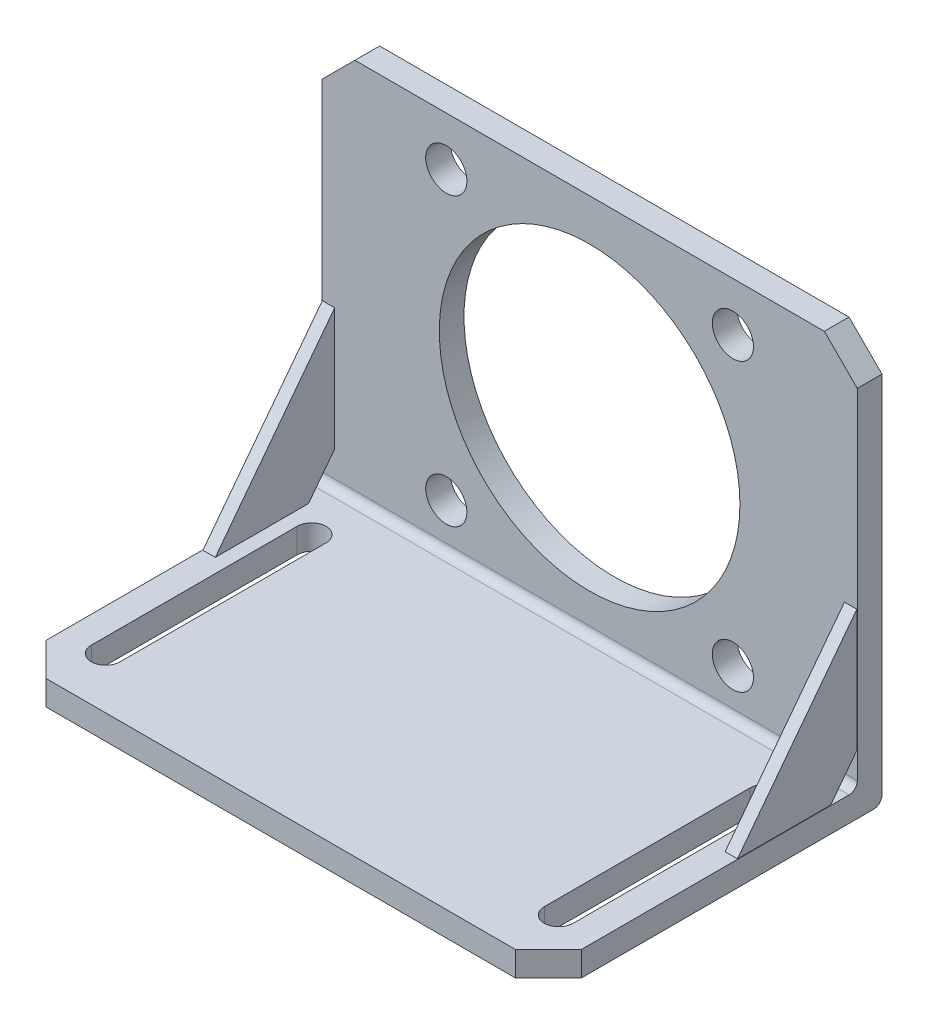
SolidWorks part; units mm, degrees
ref_plane "Front Plane" through (0, 0, 0) normal (0, 0, 1) x (1, 0, 0)
ref_plane "Top Plane" through (0, 0, 0) normal (0, 1, 0) x (1, 0, 0)
ref_plane "Right Plane" through (0, 0, 0) normal (1, 0, 0) x (0, 0, -1)
sketch "Sketch1" plane through (0, 0, 0) normal (0, 0, 1) x (1, 0, 0)
  line L1 (-65.4, -6.042) -> (64.6, -6.042)
  line L2 (-65.4, -6.042) -> (-65.4, 92.458)
  line L3 (-65.4, 92.458) -> (64.6, 92.458)
  line L4 (64.6, -6.042) -> (64.6, 92.458)
  line L6 (-0.4, 91.658) -> (-0.4, -0.042) construction
  line L8 (-35.2, 80.608) -> (34.4, 80.608) construction
  line L9 (-35.2, 80.608) -> (-35.2, 11.008) construction
  line L10 (-35.2, 11.008) -> (34.4, 11.008) construction
  line L11 (34.4, 80.608) -> (34.4, 11.008) construction
  line L12 (-35.2, 80.608) -> (34.4, 11.008) construction
  line L13 (-35.2, 11.008) -> (34.4, 80.608) construction
  circle A0 centre (-0.4, 45.808) radius 36.5
  circle A1 centre (-35.2, 80.608) radius 5
  circle A2 centre (34.4, 80.608) radius 5
  circle A3 centre (34.4, 11.008) radius 5
  circle A4 centre (-35.2, 11.008) radius 5
  arc A5 (34.4, 83.908) -> (34.4, 77.308) centre (34.4, 80.608) ccw construction
  arc A8 (34.4, 14.308) -> (34.4, 7.708) centre (34.4, 11.008) ccw construction
  arc A9 (-35.2, 83.908) -> (-35.2, 77.308) centre (-35.2, 80.608) ccw construction
  arc A10 (34.4, 8.208) -> (34.4, 13.808) centre (34.4, 11.008) ccw construction
  arc A11 (-35.2, 14.308) -> (-35.2, 7.708) centre (-35.2, 11.008) ccw construction
  point P4 (-0.4, -6.042)
  point P5 (0, 0)
  point P6 (0, 0)
  point P19 (0, 0)
  point P20 (0, 0)
  point P27 (0, 49.25)
  point P28 (-0.6, 45.808)
  dimension "D4" = 73
  dimension "D5" = 10
  dimension "D1" = 130
extrude "Boss-Extrude1" add sketch "Sketch1" along normal blind 6
sketch "Sketch2" plane through (0, 0, 6) normal (0, 0, 1) x (1, 0, 0)
  line L0 (64.6, -6.042) -> (64.6, 92.458) construction
  line L1 (-65.4, -6.042) -> (64.6, -6.042)
  line L2 (-65.4, -6.042) -> (-65.4, -0.042)
  line L3 (-65.4, -0.042) -> (64.6, -0.042)
  line L4 (64.6, -6.042) -> (64.6, -0.042)
  dimension "D1" = 6
extrude "Boss-Extrude2" add sketch "Sketch2" along normal blind 75
chamfer "Chamfer1" distance 8 angle 45 4 edges at (64.6, -3.042, 81) (-65.4, -3.042, 81) (64.6, 92.458, 3) (-65.4, 92.458, 3)
sketch "Sketch3" plane through (0, -0.042, 0) normal (0, 1, 0) x (1, 0, 0)
  line L0 (-55.4, -6) -> (-55.4, -81) construction
  line L1 (64.6, -6) -> (-65.4, -6) construction
  line L2 (56.6, -81) -> (-57.4, -81) construction
  line L3 (-55.4, -68.5) -> (-55.4, -18.5) construction
  line L4 (-58.9, -68.5) -> (-58.9, -18.5)
  line L5 (-51.9, -68.5) -> (-51.9, -18.5)
  line L6 (-0.4, -6) -> (-0.4, -81) construction
  line L7 (54.6, -68.5) -> (54.6, -18.5) construction
  line L8 (58.1, -68.5) -> (58.1, -18.5)
  line L9 (51.1, -68.5) -> (51.1, -18.5)
  line L10 (64.6, -73) -> (64.6, -6) construction
  arc A0 (-58.9, -68.5) -> (-51.9, -68.5) centre (-55.4, -68.5) ccw
  arc A1 (-51.9, -18.5) -> (-58.9, -18.5) centre (-55.4, -18.5) ccw
  arc A2 (58.1, -68.5) -> (51.1, -68.5) centre (54.6, -68.5) cw
  arc A3 (51.1, -18.5) -> (58.1, -18.5) centre (54.6, -18.5) cw
  point P8 (-55.4, -43.5)
  point P17 (54.6, -43.5)
  dimension "D1" = 7
  dimension "D2" = 50
  dimension "D3" = 10
extrude "Cut-Extrude1" cut sketch "Sketch3" against normal through all
sketch "Sketch4" plane through (-65.4, 0, 0) normal (-1, 0, 0) x (0, 0, 1)
  line L0 (6, 37.958) -> (35, -0.042)
  line L1 (6, 84.458) -> (6, -0.042) construction
  line L2 (73, -0.042) -> (6, -0.042) construction
  line L3 (35, -0.042) -> (12.3571, -0.042)
  line L4 (6, 8.2879) -> (6, 37.958)
  line L5 (6, 8.2879) -> (12.3571, -0.042)
  dimension "D3" = 18
extrude "Boss-Extrude3" add sketch "Sketch4" against normal blind 3 from offset 0.1 offset against normal yes
sketch "Sketch5" plane through (64.6, 0, 0) normal (1, 0, 0) x (0, 0, -1)
  line L3 (-6, 8.2879) -> (-6, 37.958)
  line L4 (-6, 37.958) -> (-35, -0.042)
  line L5 (-35, -0.042) -> (-12.3571, -0.042)
  line L6 (-6, 8.2879) -> (-6, 37.958)
  line L7 (-6, 37.958) -> (-35, -0.042)
  line L8 (-35, -0.042) -> (-12.3571, -0.042)
  line L10 (-12.3571, -0.042) -> (-6, 8.2879)
  line L11 (-12.3571, -0.042) -> (-6, 8.2879)
  dimension "D1" = 0
extrude "Boss-Extrude4" add sketch "Sketch5" against normal blind 3 from offset 0.1 offset against normal yes
fillet "Fillet1" radius 2 2 edges at (-0.4, -6.042, 0) (-0.4, -0.042, 6)
